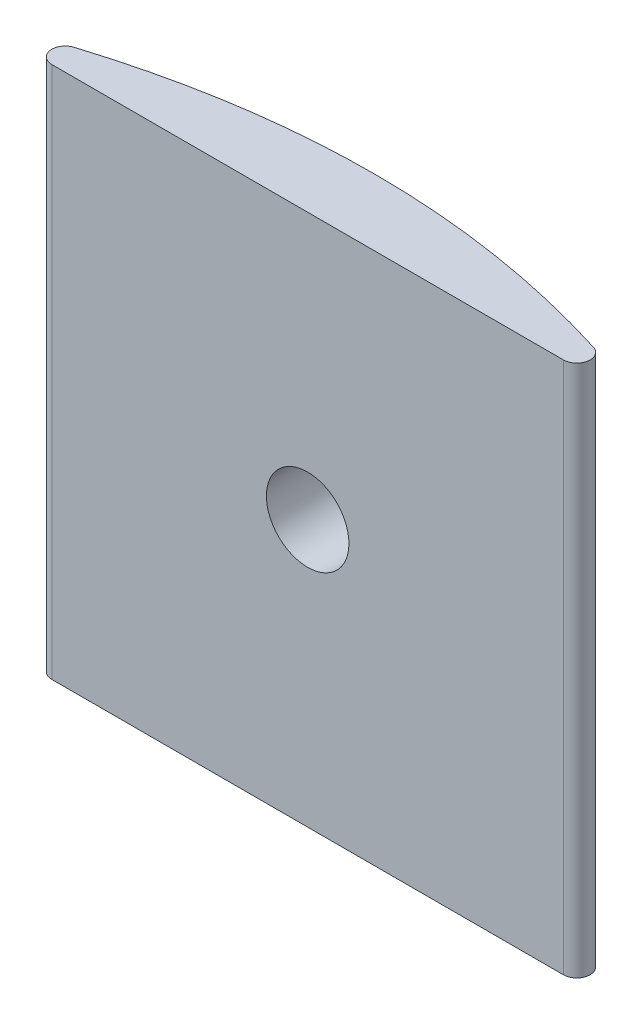
SolidWorks part; units mm, degrees
ref_plane "Front Plane" through (0, 0, 0) normal (0, 0, 1) x (1, 0, 0)
ref_plane "Top Plane" through (0, 0, 0) normal (0, 1, 0) x (1, 0, 0)
ref_plane "Right Plane" through (0, 0, 0) normal (1, 0, 0) x (0, 0, -1)
sketch "Sketch1" plane through (0, 0, 0) normal (0, 1, 0) x (1, 0, 0)
  line L0 (0, 0) -> (0, 2.5) construction
  line L1 (0, 0) -> (25, 0)
  line L2 (12.5, 0) -> (12.5, 2.5)
  spline S0 degree 2 poles (0, 0) (12.5, 5) (25, 0) knots 0 0 0 1 1 1
  dimension "D1" = 2.5
  dimension "D2" = 25
extrude "Boss-Extrude1" add sketch "Sketch1" along normal blind 20 contours S0 L2 L1 | S0 L1 L2
sketch "Sketch2" plane through (0, 0, 0) normal (0, 0, 1) x (1, 0, 0)
  line L0 (25, 20) -> (25, 0) construction
  line L2 (0, 0) -> (25, 0) construction
  circle A0 centre (12.5, 10) radius 1.55
  dimension "D3" = 3.1
  dimension "D1" = 12.5
  dimension "D2" = 10
extrude "Cut-Extrude1" cut sketch "Sketch2" against normal blind 20
fillet "Fillet1" radius 0.5 2 edges at (0, 10, 0) (25, 10, 0)
